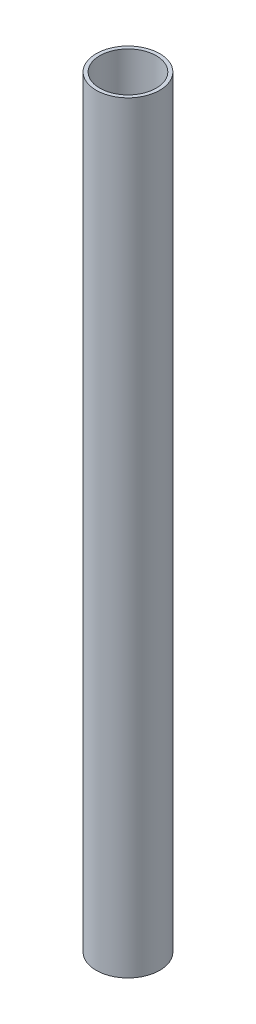
SolidWorks part; units mm, degrees
ref_plane "Front Plane" through (0, 0, 0) normal (0, 0, 1) x (1, 0, 0)
ref_plane "Top Plane" through (0, 0, 0) normal (0, 1, 0) x (1, 0, 0)
ref_plane "Right Plane" through (0, 0, 0) normal (1, 0, 0) x (0, 0, -1)
sketch "Sketch1" plane through (0, 0, 0) normal (0, 1, 0) x (1, 0, 0)
  circle A0 centre (0, 0) radius 6.35
  circle A1 centre (0, 0) radius 5.6388
  dimension "D1" = 12.7
  dimension "D2" = 11.2776
extrude "Boss-Extrude1" add sketch "Sketch1" along normal blind 152.4
